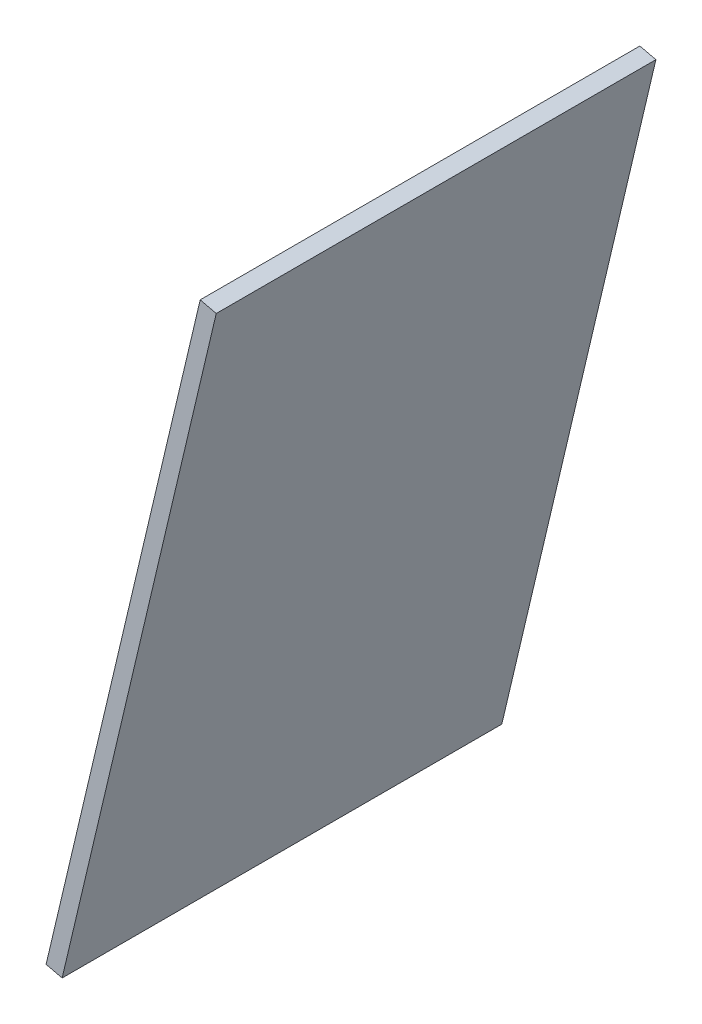
SolidWorks part; units mm, degrees
ref_plane "Front Plane" through (0, 0, 0) normal (0, 0, 1) x (1, 0, 0)
ref_plane "Top Plane" through (0, 0, 0) normal (0, 1, 0) x (1, 0, 0)
ref_plane "Right Plane" through (0, 0, 0) normal (1, 0, 0) x (0, 0, -1)
sketch "Sketch2" plane through (-379.283, -1272.3636, 6580.7646) normal (-0.9732, 0.2298, 0) x (0.2298, 0.9732, 0)
  line L1 (256.0617, 378.6945) -> (134.0617, 378.6945)
  line L2 (256.0617, 378.6945) -> (256.0617, 458.6945)
  line L3 (256.0617, 458.6945) -> (134.0617, 458.6945)
  line L4 (134.0617, 378.6945) -> (134.0617, 458.6945)
  dimension "D1" = 122
extrude "Boss-Extrude1" add sketch "Sketch2" along normal blind 3
